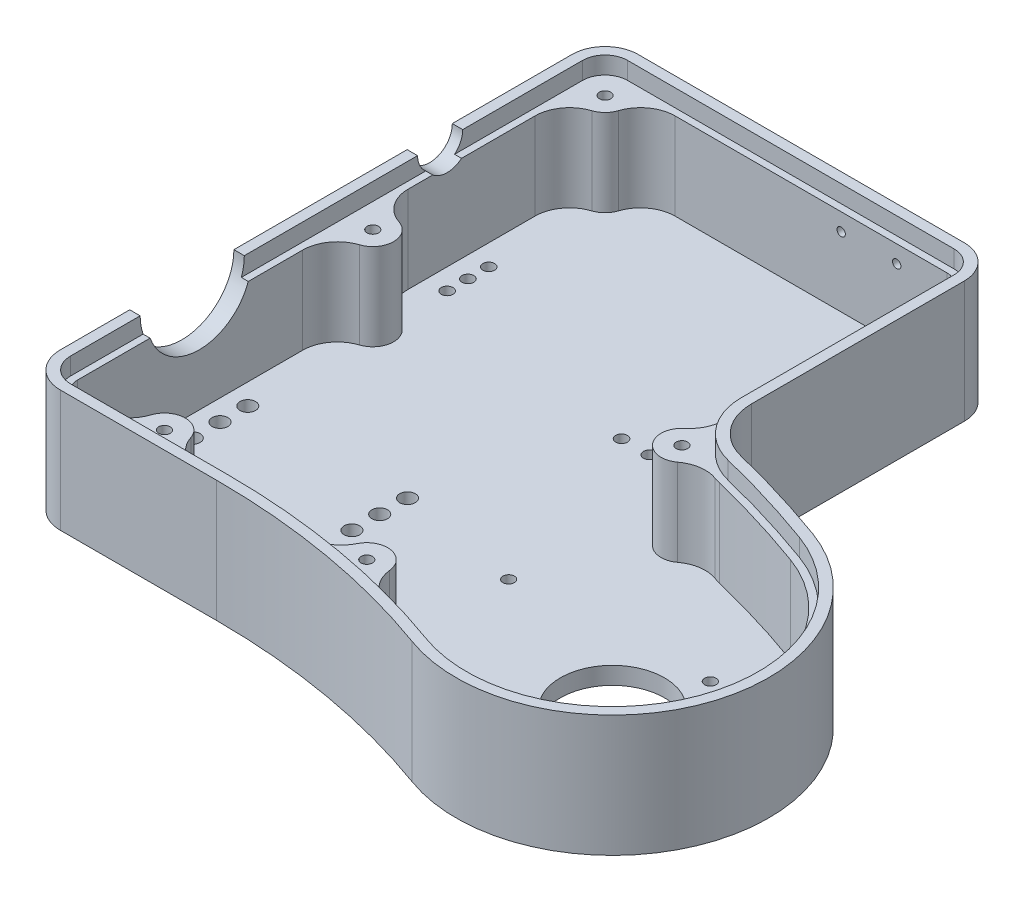
SolidWorks part; units mm, degrees
ref_plane "정면" through (0, 0, 0) normal (0, 0, 1) x (1, 0, 0)
ref_plane "윗면" through (0, 0, 0) normal (0, 1, 0) x (1, 0, 0)
ref_plane "우측면" through (0, 0, 0) normal (1, 0, 0) x (0, 0, -1)
sketch "스케치1" plane through (0, 0, 0) normal (0, 1, 0) x (1, 0, 0)
  line L0 (0, 0) -> (0, 23630.4906) construction
  line L1 (0, 0) -> (23630.4906, 0) construction
  line L2 (10, 1142.033) -> (10, 121.9) construction
  line L3 (10, -245) -> (78.404, -57.0615) construction
  line L4 (-35.5, 121.9) -> (10, 121.9)
  line L5 (-45, 112.4) -> (-45, -35)
  line L6 (-35, -45) -> (10, -45)
  line L9 (109.1858, 27.5109) -> (17111.0072, 46739.631) construction
  line L10 (10, 121.9) -> (58.5, 121.9)
  line L13 (68, 112.4) -> (68, 51.1351)
  line L14 (10, -45) -> (10, -23528.7236) construction
  arc A0 (78.404, -57.0615) -> (10, -45) centre (10, -245) ccw
  arc A2 (109.1858, 27.5109) -> (79.4098, 36.5711) centre (10, -245) ccw
  arc A3 (78.404, -57.0615) -> (109.1858, 27.5109) centre (93.7949, -14.7753) ccw
  arc A4 (-45, -35) -> (-35, -45) centre (-35, -35) ccw
  arc A5 (-35.5, 121.9) -> (-45, 112.4) centre (-35.5, 112.4) ccw
  arc A6 (58.5, 121.9) -> (68, 112.4) centre (58.5, 112.4) cw
  arc A7 (68, 51.1351) -> (79.4098, 36.5711) centre (83, 51.1351) ccw
  point P19 (-45, -45)
  point P24 (-45, 121.9)
  point P27 (68, 121.9)
  dimension "D5" = 400
  dimension "D6" = 90
  dimension "D9" = 10
  dimension "D10" = 9.5
  dimension "D11" = 9.5
  dimension "D12" = 15
  dimension "D1" = 10
  dimension "D2" = 55
  dimension "D3" = 166.9
  dimension "D4" = 45
  dimension "D7" = 20
  dimension "D8" = 58
extrude "보스-돌출1" add sketch "스케치1" along normal blind 35
sketch "스케치2" plane through (0, 35, 0) normal (0, 1, 0) x (1, 0, 0)
  line L8 (-40, 112.4) -> (-40, -35)
  line L9 (-35, -40) -> (10, -40)
  line L10 (63, 51.1351) -> (63, 112.4)
  line L11 (58.5, 116.9) -> (-35.5, 116.9)
  line L12 (-40, 112.4) -> (-40, -35)
  line L13 (-35, -40) -> (10, -40)
  line L14 (63, 51.1351) -> (63, 112.4)
  line L15 (58.5, 116.9) -> (-35.5, 116.9)
  arc A6 (80.1141, -52.363) -> (10, -40) centre (10, -245) ccw
  arc A7 (80.1141, -52.363) -> (107.4757, 22.8124) centre (93.7949, -14.7753) ccw
  arc A8 (107.4757, 22.8124) -> (78.2131, 31.7164) centre (10, -245) ccw
  arc A9 (80.1141, -52.363) -> (10, -40) centre (10, -245) ccw
  arc A10 (80.1141, -52.363) -> (107.4757, 22.8124) centre (93.7949, -14.7753) ccw
  arc A11 (107.4757, 22.8124) -> (78.2131, 31.7164) centre (10, -245) ccw
  arc A12 (63, 112.4) -> (58.5, 116.9) centre (58.5, 112.4) ccw
  arc A14 (-35.5, 116.9) -> (-40, 112.4) centre (-35.5, 112.4) ccw
  arc A15 (-35.5, 116.9) -> (-40, 112.4) centre (-35.5, 112.4) ccw
  arc A16 (-40, -35) -> (-35, -40) centre (-35, -35) ccw
  arc A17 (-40, -35) -> (-35, -40) centre (-35, -35) ccw
  arc A18 (63, 112.4) -> (58.5, 116.9) centre (58.5, 112.4) ccw
  arc A20 (63, 51.1351) -> (78.2131, 31.7164) centre (83, 51.1351) ccw
  arc A21 (63, 51.1351) -> (78.2131, 31.7164) centre (83, 51.1351) ccw
  dimension "D1" = 5
extrude "컷-돌출1" cut sketch "스케치2" against normal blind 30
sketch "스케치3" plane through (0, 0, 0) normal (0, -1, 0) x (1, 0, 0)
  line L0 (93.7949, 14.7753) -> (17194.8021, -46969.8557) construction
  line L1 (93.7949, 14.7753) -> (47078.426, 17115.7825) construction
  circle A0 centre (93.7949, 14.7753) radius 15
  circle A1 centre (86.2705, 35.4485) radius 2 construction
  circle A2 centre (112.5888, 21.6157) radius 2 construction
  circle A3 centre (101.3194, -5.8979) radius 2 construction
  circle A4 centre (46.8103, -2.3257) radius 2 construction
  point P15 (0, 0)
  dimension "D1" = 30
  dimension "D3" = 4
  dimension "D4" = 4
  dimension "D5" = 4
  dimension "D9" = 4
  dimension "D2" = 45
  dimension "D6" = 22
  dimension "D7" = 22
  dimension "D8" = 20
  dimension "D10" = 50
sketch "스케치4" plane through (-45, 0, 0) normal (-1, 0, 0) x (0, 0, 1)
  line L0 (-112.4, 35) -> (35, 35) construction
  line L1 (35, 35) -> (35, 0) construction
  circle A0 centre (0, 35) radius 15
  dimension "D1" = 30
  dimension "D2" = 35
extrude "컷-돌출3" cut sketch "스케치4" against normal blind 10 contours A0
sketch "스케치9" plane through (-45, 0, 0) normal (-1, 0, 0) x (0, 0, 1)
  line L1 (-112.4, 35) -> (-15, 35) construction
  line L2 (35, 35) -> (35, 0) construction
  circle A0 centre (-71.4, 35) radius 6.5
  dimension "D1" = 13
  dimension "D2" = 106.4
extrude "컷-돌출6" cut sketch "스케치9" against normal blind 5
sketch "스케치12" plane through (0, 0, -121.9) normal (0, 0, -1) x (-1, 0, 0)
  line L0 (-0.4277, 35) -> (49999.5723, 35) construction
  line L2 (-63, 35) -> (-63, 50035) construction
  line L3 (-68, 35) -> (-68, 0) construction
  line L5 (-63, 25) -> (49937, 25) construction
  line L6 (-44, 45) -> (-44, -49955) construction
  line L7 (-28, 45) -> (-28, -49955) construction
  circle A2 centre (-44, 25) radius 1.2
  circle A3 centre (-28, 25) radius 1.2
  dimension "D2" = 2.4
  dimension "D5" = 2.4
  dimension "D1" = 5
  dimension "D7" = 10
  dimension "D8" = 19
  dimension "D9" = 35
extrude "컷-돌출8" cut sketch "스케치12" against normal up to next
sketch "스케치13" plane through (0, 35, 0) normal (0, 1, 0) x (1, 0, 0)
  line L0 (-42, -35) -> (-42, -28.0869)
  line L1 (-40, -28.0869) -> (-40, -35)
  line L6 (58.5, 118.9) -> (-35.5, 118.9)
  line L7 (-42, 112.4) -> (-42, 77.9)
  line L8 (58.5, 118.9) -> (-35.5, 118.9)
  line L9 (-42, 112.4) -> (-42, 77.9)
  line L15 (58.5, 116.9) -> (-35.5, 116.9)
  line L16 (-40, 112.4) -> (-40, 77.9)
  line L17 (58.5, 116.9) -> (-35.5, 116.9)
  line L18 (-40, 112.4) -> (-40, 77.9)
  line L23 (-35, -40) -> (10, -40)
  line L24 (63, 51.1351) -> (63, 112.4)
  line L25 (-35, -40) -> (10, -40)
  line L26 (63, 51.1351) -> (63, 112.4)
  line L37 (-42, 64.9) -> (-42, 15)
  line L38 (-42, 64.9) -> (-42, -28.0869)
  line L40 (-40, 64.9) -> (-40, 15)
  line L41 (-40, 64.9) -> (-40, -28.0869)
  line L43 (-42, 77.9) -> (-42, 64.9)
  line L44 (-40, 64.9) -> (-40, 77.9)
  line L47 (-35, -42) -> (10, -42)
  line L48 (65, 51.1351) -> (65, 112.4)
  line L49 (-35, -42) -> (10, -42)
  line L50 (65, 51.1351) -> (65, 112.4)
  arc A2 (65, 112.4) -> (58.5, 118.9) centre (58.5, 112.4) ccw
  arc A3 (-35.5, 118.9) -> (-42, 112.4) centre (-35.5, 112.4) ccw
  arc A4 (-35.5, 118.9) -> (-42, 112.4) centre (-35.5, 112.4) ccw
  arc A5 (65, 112.4) -> (58.5, 118.9) centre (58.5, 112.4) ccw
  arc A7 (-35.5, 116.9) -> (-40, 112.4) centre (-35.5, 112.4) ccw
  arc A8 (-35.5, 116.9) -> (-40, 112.4) centre (-35.5, 112.4) ccw
  arc A9 (63, 112.4) -> (58.5, 116.9) centre (58.5, 112.4) ccw
  arc A10 (63, 112.4) -> (58.5, 116.9) centre (58.5, 112.4) ccw
  arc A40 (-40, -35) -> (-35, -40) centre (-35, -35) ccw
  arc A41 (80.1141, -52.363) -> (10, -40) centre (10, -245) ccw
  arc A42 (80.1141, -52.363) -> (107.4757, 22.8124) centre (93.7949, -14.7753) ccw
  arc A43 (107.4757, 22.8124) -> (78.2131, 31.7164) centre (10, -245) ccw
  arc A44 (63, 51.1351) -> (78.2131, 31.7164) centre (83, 51.1351) ccw
  arc A45 (-40, -35) -> (-35, -40) centre (-35, -35) ccw
  arc A46 (80.1141, -52.363) -> (10, -40) centre (10, -245) ccw
  arc A47 (80.1141, -52.363) -> (107.4757, 22.8124) centre (93.7949, -14.7753) ccw
  arc A48 (107.4757, 22.8124) -> (78.2131, 31.7164) centre (10, -245) ccw
  arc A52 (63, 51.1351) -> (78.2131, 31.7164) centre (83, 51.1351) ccw
  arc A54 (-42, -35) -> (-35, -42) centre (-35, -35) ccw
  arc A55 (79.4301, -54.2424) -> (10, -42) centre (10, -245) ccw
  arc A56 (79.4301, -54.2424) -> (108.1598, 24.6918) centre (93.7949, -14.7753) ccw
  arc A57 (108.1598, 24.6918) -> (78.6918, 33.6583) centre (10, -245) ccw
  arc A58 (65, 51.1351) -> (78.6918, 33.6583) centre (83, 51.1351) ccw
  arc A59 (-42, -35) -> (-35, -42) centre (-35, -35) ccw
  arc A60 (79.4301, -54.2424) -> (10, -42) centre (10, -245) ccw
  arc A61 (79.4301, -54.2424) -> (108.1598, 24.6918) centre (93.7949, -14.7753) ccw
  arc A62 (108.1598, 24.6918) -> (78.6918, 33.6583) centre (10, -245) ccw
  arc A63 (65, 51.1351) -> (78.6918, 33.6583) centre (83, 51.1351) ccw
  dimension "D1" = 2
  dimension "D2" = 0
  dimension "D3" = 2
  dimension "D4" = 0
  dimension "D5" = 2
  dimension "D6" = 0
  dimension "D7" = 2
  dimension "D8" = 0
extrude "컷-돌출9" cut sketch "스케치13" against normal blind 5
sketch "스케치14" plane through (0, 5, 0) normal (0, 1, 0) x (1, 0, 0)
  line L0 (-78.9839, 57.65) -> (49921.0161, 57.65) construction
  line L6 (58.5, 116.9) -> (-35.5, 116.9) construction
  line L7 (14, 107.5) -> (14, -49892.5) construction
  line L8 (14, 53.65) -> (50014, 53.65) construction
  line L9 (36, 74.4851) -> (36, -49925.5149) construction
  line L10 (28, 79.5678) -> (28, -49920.4322) construction
  line L11 (44, 80.5487) -> (44, -49919.4513) construction
  line L12 (-45, 112.4) -> (-45, 77.9) construction
  circle A0 centre (36, 53.65) radius 1.7
  circle A1 centre (28, 53.65) radius 1.7
  circle A2 centre (44, 53.65) radius 1.7
  dimension "D3" = 3.4
  dimension "D4" = 3.4
  dimension "D5" = 3.4
  dimension "D1" = 59
  dimension "D2" = 59.25
  dimension "D6" = 4
  dimension "D7" = 22
  dimension "D8" = 14
  dimension "D9" = 30
extrude "컷-돌출10" cut sketch "스케치14" against normal up to next
sketch "스케치15" plane through (0, 0, 0) normal (0, -1, 0) x (1, 0, 0)
  line L0 (-45, 35) -> (49955, 35) construction
  line L1 (-92.1258, -71.4) -> (49907.8742, -71.4) construction
  line L2 (-45, -112.4) -> (-45, 35) construction
  line L3 (-38, -50) -> (-30, -50) construction
  line L4 (-38, -50) -> (-38, -70) construction
  line L5 (-38, -70) -> (-30, -70) construction
  line L6 (-30, -50) -> (-30, -70) construction
  line L7 (-34, -50) -> (-34, -50050) construction
  circle A0 centre (-34, -65.4) radius 1.7
  circle A1 centre (-34, -71.4) radius 1.7
  circle A2 centre (-34, -77.4) radius 1.7
  point P5 (-26.4355, -71.4)
  point P10 (-34, -70)
  point P21 (-34, -50)
  dimension "D5" = 3.4
  dimension "D6" = 3.4
  dimension "D7" = 3.4
  dimension "D1" = 106.4
  dimension "D2" = 8
  dimension "D3" = 20
  dimension "D4" = 7
  dimension "D8" = 6
  dimension "D9" = 6
extrude "컷-돌출11" cut sketch "스케치15" against normal blind 5
sketch "스케치21" plane through (0, 5, 0) normal (0, 1, 0) x (1, 0, 0)
  line L0 (-45, 19.7408) -> (-45, 50019.7408) construction
  line L1 (-44.2391, 45) -> (49955.7609, 45) construction
  line L3 (67.2561, 38.801) -> (39426.8843, 30874.1649) construction
  line L4 (45.5979, -43.1144) -> (-49194.7898, 8639.2945) construction
  line L5 (25.4987, 121.9) -> (50025.4987, 121.9) construction
  line L6 (67.2561, 38.801) -> (-30768.1078, 39398.4291) construction
  line L7 (-7.9372, -45) -> (-50007.9372, -45) construction
  line L8 (45.5979, -43.1144) -> (8728.0068, 49197.2732) construction
  line L10 (136.0811, -30.1662) -> (17237.0883, 46954.4648) construction
  circle A0 centre (-35, 111.9) radius 6
  arc A1 (78.404, -57.0615) -> (109.1858, 27.5109) centre (93.7949, -14.7753) ccw construction
  circle A2 centre (-15, -35) radius 6
  circle A3 centre (-35, 45) radius 6
  arc A4 (80.1141, -52.363) -> (10, -40) centre (10, -245) ccw construction
  arc A5 (63, 51.1351) -> (78.2131, 31.7164) centre (83, 51.1351) ccw construction
  circle A6 centre (63.3202, 35.7174) radius 6
  circle A7 centre (46.4661, -38.1904) radius 6
  arc A8 (80.1141, -52.363) -> (10, -40) centre (10, -245) ccw construction
  point P18 (136.0811, -30.1662)
  point P31 (45.5979, -43.1144)
  point P36 (67.2561, 38.801)
  dimension "D1" = 12
  dimension "D4" = 12
  dimension "D7" = 12
  dimension "D9" = 12
  dimension "D11" = 12
  dimension "D2" = 10
  dimension "D3" = 10
  dimension "D5" = 30
  dimension "D6" = 10
  dimension "D8" = 10
  dimension "D10" = 5
  dimension "D12" = 5
  dimension "D13" = 90
extrude "보스-돌출7" add sketch "스케치21" along normal blind 25
fillet "필렛1" radius 10 6 edges at (69.2537, 17.5, -36.6079) (65.6049, 17.5, -41.2654) (42.3663, 17.5, 42.5712) (48.8203, 17.5, 43.7092) (-31.6834, 17.5, -116.9) (-40, 17.5, -108.5834)
sketch "스케치22" plane through (0, 30, 0) normal (0, 1, 0) x (1, 0, 0)
  line L0 (-45, 107.0854) -> (-45, 50107.0854) construction
  line L2 (-31.863, 121.9) -> (-50031.863, 121.9) construction
  line L4 (-43.5, 45) -> (-50043.5, 45) construction
  line L6 (-30.4512, -45) -> (-50030.4512, -45) construction
  line L8 (45.2506, -45.084) -> (49285.6382, -8727.4929) construction
  line L9 (68.8305, 40.0344) -> (30904.1945, -39319.5938) construction
  line L10 (43.8341, -53.1173) -> (8726.243, 49187.2704) construction
  line L11 (48.8558, 24.3857) -> (39408.484, 30859.7497) construction
  arc A1 (79.4301, -54.2424) -> (10, -42) centre (10, -245) ccw construction
  arc A2 (65, 51.1351) -> (78.6918, 33.6583) centre (83, 51.1351) ccw construction
  arc A3 (52.4316, -37.5478) -> (41.0802, -35.5462) centre (46.4661, -38.1904) ccw construction
  arc A4 (59.5088, 40.3514) -> (66.9072, 30.9077) centre (63.3202, 35.7174) ccw construction
  circle A6 centre (-35, 111.9) radius 2
  circle A7 centre (-35, 45) radius 2
  circle A8 centre (-15, -35) radius 2
  circle A9 centre (46.4661, -38.1904) radius 2
  circle A10 centre (63.3202, 35.7174) radius 2
  point P17 (45.2506, -45.084)
  point P23 (68.8305, 40.0344)
  point P31 (47.508, -32.2815)
  point P37 (58.597, 32.0172)
  dimension "D1" = 4
  dimension "D4" = 4
  dimension "D6" = 4
  dimension "D9" = 4
  dimension "D11" = 4
  dimension "D2" = 10
  dimension "D3" = 10
  dimension "D5" = 10
  dimension "D7" = 30
  dimension "D8" = 10
  dimension "D10" = 7
  dimension "D12" = 7
  dimension "D13" = 90
fillet "필렛2" radius 10 2 edges at (-40, 17.5, -48.3166) (-40, 17.5, -41.6834)
fillet "필렛3" radius 10 2 edges at (-18.3166, 17.5, 40) (-11.6834, 17.5, 40)
sketch "스케치23" plane through (0, 5, 0) normal (0, 1, 0) x (1, 0, 0)
  line L0 (12, 29.4533) -> (12, -49970.5467) construction
  line L1 (-40, 29.8013) -> (-40, -35) construction
  line L2 (-63.3193, 0) -> (49936.6807, 0) construction
  line L4 (-45, -35) -> (49955, -35) construction
  circle A0 centre (12, 0) radius 2.25
  circle A1 centre (12, -8) radius 2.25
  circle A2 centre (12, 8) radius 2.25
  dimension "D3" = 4.5
  dimension "D4" = 4.5
  dimension "D5" = 4.5
  dimension "D1" = 52
  dimension "D2" = 35
  dimension "D6" = 8
  dimension "D7" = 8
extrude "컷-돌출17" cut sketch "스케치23" against normal up to next
sketch "스케치24" plane through (0, 0, 0) normal (0, -1, 0) x (1, 0, 0)
  line L0 (12, 0) -> (-49988, 0) construction
  line L1 (12, 8) -> (-49988, 8) construction
  line L2 (12, -8) -> (-49988, -8) construction
  line L3 (-34, 8) -> (-34, -49992) construction
  circle A0 centre (-34, -8) radius 2.25
  circle A1 centre (-34, 0) radius 2.25
  circle A2 centre (-34, 8) radius 2.25
  dimension "D1" = 4.5
  dimension "D2" = 4.5
  dimension "D3" = 4.5
extrude "컷-돌출18" cut sketch "스케치24" against normal through all
hole_wizard "M4 나사 구멍1" positions "스케치25" profile "스케치26" tap size "M4" standard "ISO"
sketch "스케치25" plane through (0, 30, 0) normal (0, 1, 0) x (1, 0, 0)
  point P0 (-35, 111.9)
  point P3 (-35, 45)
  point P6 (-15, -35)
  point P9 (46.4661, -38.1904)
  point P12 (63.3202, 35.7174)
sketch "스케치26" plane through (-35, 30, -111.9) normal (1, 0, 0) x (0, 0, 1)
  line L0 (0, 0) -> (0, 12.4914)
  line L1 (0, 12.4914) -> (1.65, 11.5)
  line L2 (1.65, 11.5) -> (1.65, 0)
  line L5 (1.65, 0) -> (0, 0)
  line L10 (0, 12.4914) -> (-1.65, 11.5) construction
  line L11 (0, -6.35) -> (0, 107.95) construction
  dimension "탭 드릴 지름" = 3.3
  dimension "탭 드릴 깊이" = 11.5
  dimension "드릴 각도" = 118
cosmetic thread "구멍 나사산1" parameters "D1"=8, "D2"=4
cosmetic thread "구멍 나사산2" parameters "D1"=8, "D2"=4
cosmetic thread "구멍 나사산3" parameters "D1"=8, "D2"=4
cosmetic thread "구멍 나사산4" parameters "D1"=8, "D2"=4
cosmetic thread "구멍 나사산5" parameters "D1"=8, "D2"=4
extrude "컷-돌출19" cut sketch "스케치3" against normal up to next and the other way through all
hole_wizard "M4 나사 구멍2" positions "스케치27" profile "스케치28" tap size "M4" standard "ISO"
sketch "스케치27" plane through (0, 5, 0) normal (0, 1, 0) x (1, 0, 0)
  point P0 (46.8103, 2.3257)
  point P3 (101.3194, 5.8979)
  point P6 (112.5888, -21.6157)
  point P9 (86.2705, -35.4485)
sketch "스케치28" plane through (46.8103, 5, -2.3257) normal (1, 0, 0) x (0, 0, 1)
  line L0 (0, 0) -> (0, 12.4914)
  line L1 (0, 12.4914) -> (1.65, 11.5)
  line L2 (1.65, 11.5) -> (1.65, 0)
  line L5 (1.65, 0) -> (0, 0)
  line L10 (0, 12.4914) -> (-1.65, 11.5) construction
  line L11 (0, -6.35) -> (0, 107.95) construction
  dimension "탭 드릴 지름" = 3.3
  dimension "탭 드릴 깊이" = 11.5
  dimension "드릴 각도" = 118
cosmetic thread "구멍 나사산6" parameters "D1"=5, "D2"=4
cosmetic thread "구멍 나사산7" parameters "D1"=5, "D2"=4
cosmetic thread "구멍 나사산8" parameters "D1"=5, "D2"=4
cosmetic thread "구멍 나사산9" parameters "D1"=5, "D2"=4
